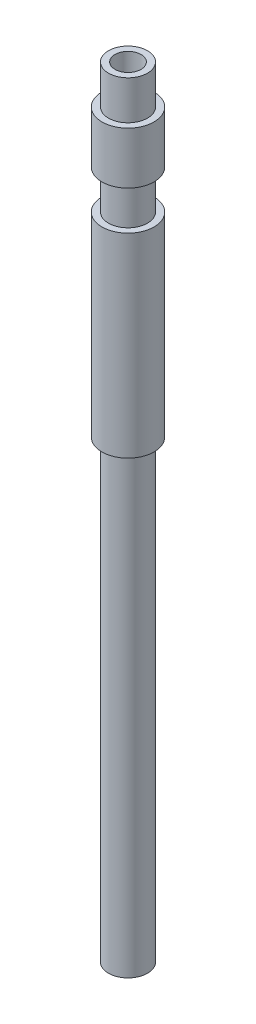
SolidWorks part; units mm, degrees
material "Простая углеродистая сталь"
ref_plane "Спереди" through (0, 0, 0) normal (0, 0, 1) x (1, 0, 0)
ref_plane "Сверху" through (0, 0, 0) normal (0, 1, 0) x (1, 0, 0)
ref_plane "Справа" through (0, 0, 0) normal (1, 0, 0) x (0, 0, -1)
sketch "Эскиз1" plane through (0, 0, 0) normal (0, 1, 0) x (1, 0, 0)
  circle A0 centre (0, 0) radius 1
  circle A1 centre (0, 0) radius 2
  dimension "D1" = 4
  dimension "D2" = 2
extrude "Бобышка-Вытянуть1" add sketch "Эскиз1" along normal blind 60
sketch "Эскиз2" plane through (0, 0, 0) normal (0, 0, 1) x (1, 0, 0)
  line L0 (2, 60) -> (1.5, 60)
  line L1 (2, 60) -> (2, 57)
  line L2 (1.5, 60) -> (1.5, 57)
  line L3 (2, 57) -> (1.5, 57)
  line L4 (2, 53) -> (1.5, 53)
  line L5 (2, 53) -> (2, 50)
  line L6 (1.5, 53) -> (1.5, 50)
  line L7 (2, 50) -> (1.5, 50)
  line L8 (1, 60) -> (-1, 60) construction
  line L9 (1, 60) -> (-1, 60) construction
  line L10 (0, 60) -> (0, 0) construction
  line L11 (-2, 0) -> (2, 0) construction
  line L12 (-2, 0) -> (2, 0) construction
  dimension "D1" = 3
  dimension "D2" = 0.5
  dimension "D3" = 2
  dimension "D4" = 7
revolve "Вырез-Повернуть1" cut sketch "Эскиз2" angle 360 about L10
sketch "Эскиз3" plane through (0, 0, 0) normal (0, 0, 1) x (1, 0, 0)
  line L0 (2, 0) -> (1.5, 0)
  line L1 (2, 0) -> (2, 35)
  line L2 (1.5, 0) -> (1.5, 35)
  line L3 (2, 35) -> (1.5, 35)
  line L4 (2, 50) -> (-2, 50) construction
  line L5 (0, 0) -> (0, 60) construction
  line L6 (1, 60) -> (-1, 60) construction
  line L7 (1, 60) -> (-1, 60) construction
  dimension "D1" = 15
  dimension "D2" = 0.5
revolve "Вырез-Повернуть2" cut sketch "Эскиз3" angle 360 about L5
sketch "Эскиз4" plane through (0, 0, 0) normal (0, 0, 1) x (1, 0, 0)
  line L0 (-2, 48) -> (2, 48) construction
  line L1 (1.5, 60) -> (-1.5, 60) construction
  line L2 (1.5, 60) -> (-1.5, 60) construction
  line L3 (2, 50) -> (-2, 50) construction
  line L4 (2, 50) -> (-2, 50) construction
  line L5 (-2, 50) -> (-2, 35) construction
  line L6 (2, 35) -> (2, 50) construction
  dimension "D1" = 12
ref_plane "Плоскость1" through (0, 48, 0) normal (0, 1, 0) x (1, 0, 0)
sketch "Эскиз5" plane through (0, 48, 0) normal (0, 1, 0) x (1, 0, 0)
  line L0 (-2, 0) -> (2, 0) construction
  circle A0 centre (0, 0) radius 2 construction
